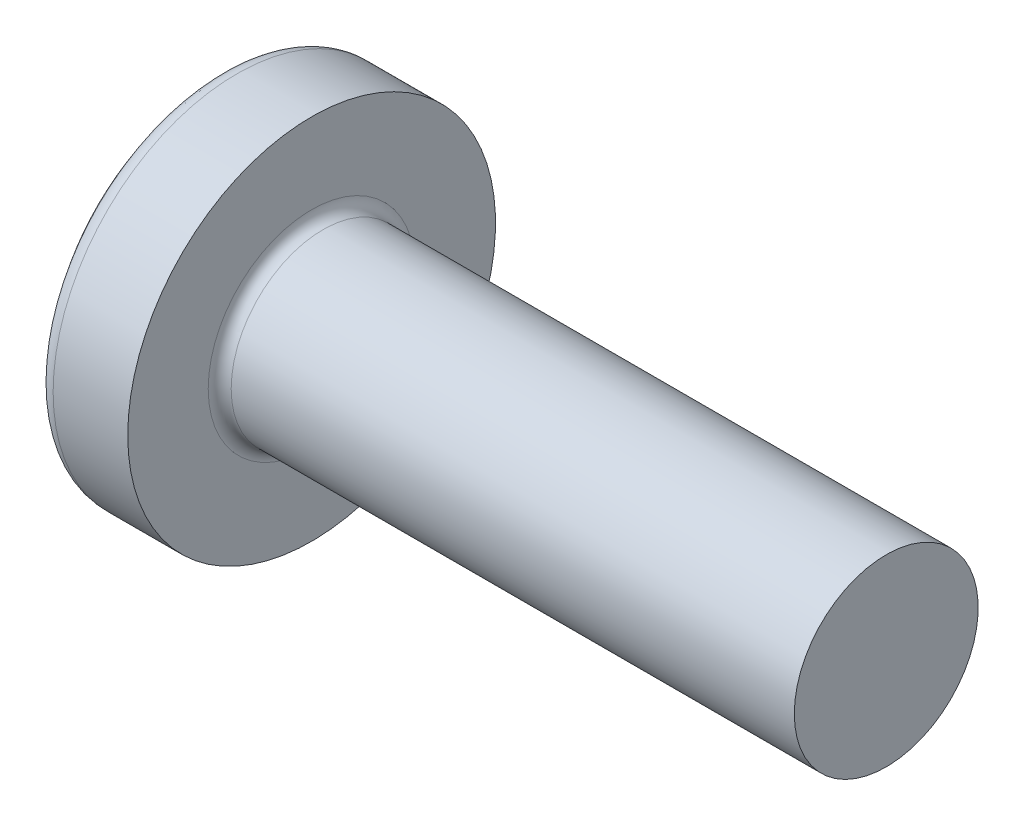
SolidWorks part; units mm, degrees
ref_plane "Plane1" through (0, 0, 0) normal (0, 0, 1) x (1, 0, 0)
ref_plane "Plane2" through (0, 0, 0) normal (0, 1, 0) x (1, 0, 0)
ref_plane "Plane3" through (0, 0, 0) normal (1, 0, 0) x (0, 0, -1)
sketch "BodySke" plane through (0, 0, 0) normal (0, 0, 1) x (1, 0, 0)
  line L0 (1.3, 0.8) -> (1.3, 1.6)
  line L1 (1.475, 6.35) -> (1.475, -3.175) construction
  line L2 (-25.4, 0) -> (127, 0) construction
  line L3 (6.3, 0) -> (0, 0)
  line L4 (1.3, 0.8) -> (6.3, 0.8)
  line L5 (6.3, 0.8) -> (6.3, 0)
  line L6 (0.6507, 1.6) -> (1.3, 1.6)
  line L8 (1.3, 6.35) -> (1.3, -3.175) construction
  arc A0 (0.5326, 1.5426) -> (0, 0) centre (2.5, 0) ccw
  arc A2 (0.5326, 1.5426) -> (0.6507, 1.6) centre (0.6507, 1.45) cw
  dimension "Head_crown_rad" = 2.5
  dimension "Head_fillet_rad" = 0.15
  dimension "Length" = 5
  dimension "Head_ht" = 1.3
  dimension "Head_dia" = 3.2
  dimension "Advance" = 0.35
  dimension "Thread_nom" = 5
  dimension "Diameter" = 1.6
revolve "Base-Revolve" add sketch "BodySke"
cosmetic thread "ThreadCosmetic" [suppressed]
fillet "Fillet1" radius 0.1 1 edges at (1.3, 0, 0.8)
sketch "Sketch3" plane through (0, 0, 0) normal (1, 0, 0) x (0, 0, -1)
  line L0 (0.24, -0.8) -> (-0.24, -0.8)
  line L1 (0.24, -0.8) -> (0.24, 0.8)
  line L2 (-0.24, 0.8) -> (0.24, 0.8)
  line L3 (-0.24, 0.8) -> (-0.24, -0.8)
  dimension "Cross_dia" = 1.6
  dimension "D1" = 0.8
  dimension "Cross_width" = 0.48
  dimension "D2" = 0.24
ref_plane "Plane4" through (0.9, 0, 0) normal (1, 0, 0) x (0, 0, -1)
sketch "Sketch4" plane through (0.9, 0, 0) normal (1, 0, 0) x (0, 0, -1)
  line L0 (0.24, -0.3513) -> (-0.24, -0.3513)
  line L1 (0.24, -0.3513) -> (0.24, 0.3513)
  line L2 (-0.24, 0.3513) -> (0.24, 0.3513)
  line L3 (-0.24, 0.3513) -> (-0.24, -0.3513)
  dimension "D1" = 0.48
  dimension "D2" = 0.7026
  dimension "D3" = 0.24
  dimension "D4" = 0.3513
loft "Recess" cut profiles "Sketch3", "Sketch4"
pattern_circular "RecPat" count 2 every 90 about axis through (0, 0, 0) along (1, 0, 0) of "Recess"
sketch "RecCorSke" plane through (0, 0, 0) normal (0, 0, 1) x (1, 0, 0)
  line L0 (-3.175, 0) -> (15.875, 0) construction
  line L1 (-25.4, 0) -> (127, 0) construction
  line L2 (0, 0) -> (0, 0.4184)
  line L3 (0, 0.4184) -> (0.9, 0.3555)
  line L4 (0.9, 0.3555) -> (1.0155, 0)
  line L5 (1.0155, 0) -> (0, 0)
  dimension "Diameter" = 0.711
  dimension "Depth" = 0.9
  dimension "Draft_angle" = 4
  dimension "Bottom_angle" = 18
revolve "RecessCore" cut sketch "RecCorSke" angle 360 about L0
sketch "ThdSchSke" plane through (0, 0, 0) normal (0, 0, 1) x (1, 0, 0)
  line L0 (2, -0.601) -> (1.8607, -0.8)
  line L1 (2, -0.601) -> (2.1393, -0.8)
  line L2 (2.1393, -0.8) -> (2.1393, -1)
  line L3 (-3.175, 0) -> (5.1513, 0) construction
  line L5 (2.1393, -1) -> (1.8607, -1)
  line L6 (1.8607, -1) -> (1.8607, -0.8)
  dimension "Diameter" = 1.6
  dimension "SideAngle" = 55
  dimension "VeeAngle" = 70
  dimension "Thread_minor" = 1.202
  dimension "Overcut" = 2
  dimension "Start" = 2
revolve "ThreadSchematic" [suppressed] cut sketch "ThdSchSke" angle 360 about L3
pattern_linear "ThdSchPat" [suppressed]
equation "\"D1@Sketch3\" = \"Cross_dia@Sketch3\" / 2"
equation "\"D2@Sketch3\" = \"Cross_width@Sketch3\" / 2"
equation "\"Depth@RecCorSke\" = \"Cross_depth@Plane4\""
equation "\"D1@Sketch4\" = \"Cross_width@Sketch3\""
equation "\"D2@Sketch4\" = \"Cross_dia@Sketch3\" - 2.0 * \"Cross_depth@Plane4\" * tan(26.5  * 0.017453292)"
equation "\"D3@Sketch4\" = \"D1@Sketch4\" / 2"
equation "\"D4@Sketch4\" = \"D2@Sketch4\" / 2"
equation "\"Thread_length@ThreadCosmetic\" = ((sgn( (\"Length@BodySke\" - \"Advance@BodySke\" * 2.0 ) - \"Thread_nom@BodySke\" )-1)*( (\"Length@BodySke\" - \"Advance@BodySke\" * 2.0 ) - \"Thread_nom@BodySke\" ))/-2+ \"Thread_nom@BodySke\""
equation "\"Thread_minor@ThdSchSke\" = \"Thread_minor@ThreadCosmetic\""
equation "\"Diameter@ThdSchSke\" = \"Diameter@BodySke\""
equation "\"Overcut@ThdSchSke\" = \"Diameter@BodySke\" * 1.25"
equation "\"Start@ThdSchSke\" = \"Head_ht@BodySke\" + \"Length@BodySke\" - \"Thread_length@ThreadCosmetic\"  '---Non-countersunk---"
equation "\"Num_threads@ThdSchPat\" = int( \"Thread_length@ThreadCosmetic\" / \"Advance@BodySke\" + 0.999 )  + 1"
equation "\"Advance@ThdSchPat\" = \"Thread_length@ThreadCosmetic\" /  (\"Num_threads@ThdSchPat\" - 1) 'relax it"
